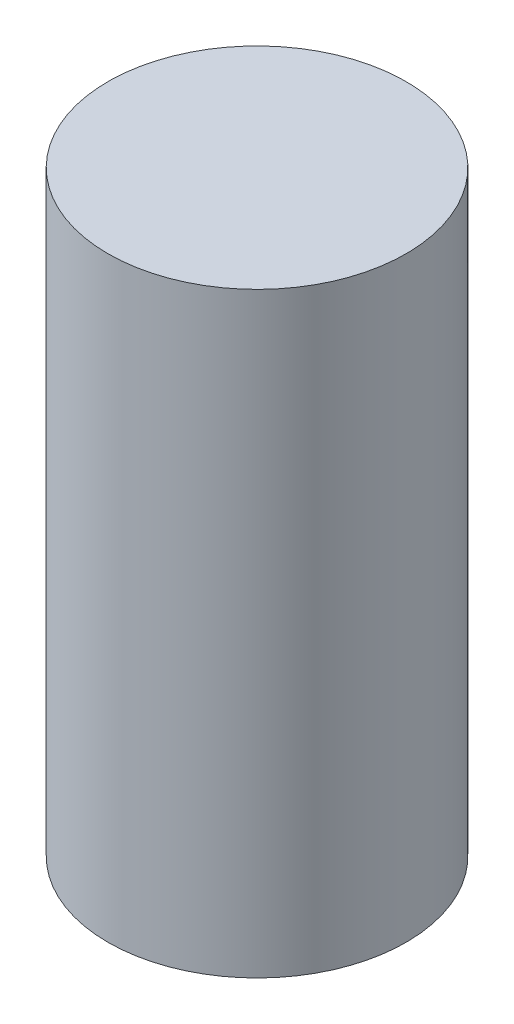
SolidWorks part; units mm, degrees
ref_plane "Front Plane" through (0, 0, 0) normal (0, 0, 1) x (1, 0, 0)
ref_plane "Top Plane" through (0, 0, 0) normal (0, 1, 0) x (1, 0, 0)
ref_plane "Right Plane" through (0, 0, 0) normal (1, 0, 0) x (0, 0, -1)
sketch "Sketch1" plane through (0, 0, 0) normal (0, 1, 0) x (1, 0, 0)
  circle A0 centre (0, 0) radius 1.5875
  dimension "D1" = 3.175
extrude "Boss-Extrude1" add sketch "Sketch1" along normal blind 6.35
